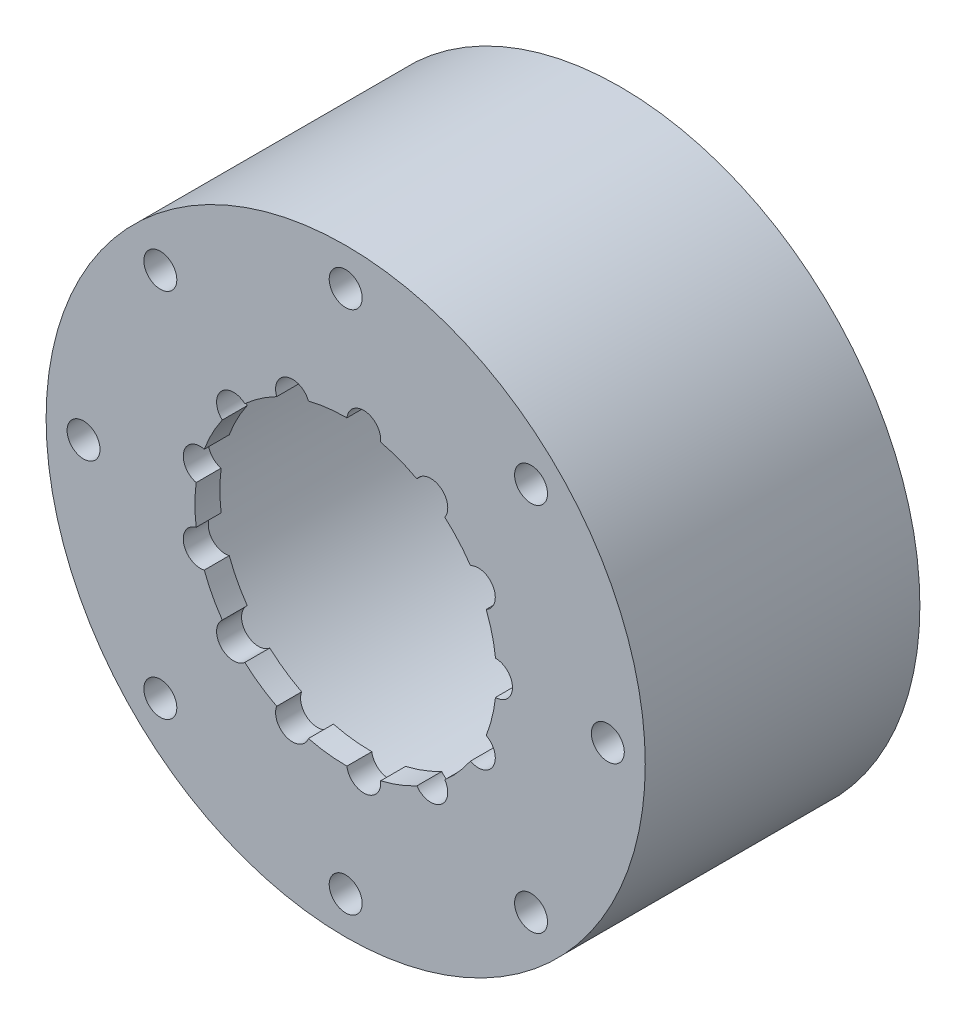
SolidWorks part; units mm, degrees
ref_plane "Front Plane" through (0, 0, 0) normal (0, 0, 1) x (1, 0, 0)
ref_plane "Top Plane" through (0, 0, 0) normal (0, 1, 0) x (1, 0, 0)
ref_plane "Right Plane" through (0, 0, 0) normal (1, 0, 0) x (0, 0, -1)
sketch "Sketch2" plane through (0, 0, 0) normal (0, 0, 1) x (1, 0, 0)
  circle A0 centre (0, 0) radius 60
  circle A1 centre (0, 0) radius 45
  dimension "D1" = 120
  dimension "D2" = 15
extrude "Boss-Extrude2" add sketch "Sketch2" along normal mid plane 50
sketch "Sketch3" plane through (0, 0, 25) normal (0, 0, 1) x (1, 0, 0)
  arc A0 (0.4234, 29.997) -> (-7.5898, 29.024) centre (0, 0) ccw construction
  circle A1 centre (0, 0) radius 60
  circle A2 centre (0, 0) radius 60
  arc A3 (29.8293, -3.1954) -> (29.8293, 3.1954) centre (30, 0) ccw construction
  arc A4 (24.9276, -16.6918) -> (27.8976, -11.033) centre (26.5637, -13.9417) ccw construction
  arc A5 (14.3152, -26.3643) -> (19.5748, -22.7338) centre (17.0419, -24.6895) ccw construction
  arc A6 (0.4234, -29.997) -> (6.7677, -29.2267) centre (3.6161, -29.7813) ccw construction
  arc A7 (-13.5654, -26.7578) -> (-7.5898, -29.024) centre (-10.6381, -28.0505) ccw construction
  arc A8 (-24.4465, -17.3887) -> (-20.2086, -22.1723) centre (-22.4553, -19.8937) ccw construction
  arc A9 (-29.7273, -4.036) -> (-28.1978, -10.2412) centre (-29.1283, -7.1795) ccw construction
  arc A10 (-28.1978, 10.2412) -> (-29.7273, 4.036) centre (-29.1283, 7.1795) ccw construction
  arc A11 (-20.2086, 22.1723) -> (-24.4465, 17.3887) centre (-22.4553, 19.8937) ccw construction
  arc A12 (-7.5898, 29.024) -> (-13.5654, 26.7578) centre (-10.6381, 28.0505) ccw construction
  arc A13 (6.7677, 29.2267) -> (0.4234, 29.997) centre (3.6161, 29.7813) ccw construction
  arc A14 (19.5748, 22.7338) -> (14.3152, 26.3643) centre (17.0419, 24.6895) ccw construction
  arc A15 (27.8976, 11.033) -> (24.9276, 16.6918) centre (26.5637, 13.9417) ccw construction
  arc A16 (14.3152, 26.3643) -> (6.7677, 29.2267) centre (0, 0) ccw construction
  arc A17 (24.9276, 16.6918) -> (19.5748, 22.7338) centre (0, 0) ccw construction
  arc A18 (29.8293, 3.1954) -> (27.8976, 11.033) centre (0, 0) ccw construction
  arc A19 (27.8976, -11.033) -> (29.8293, -3.1954) centre (0, 0) ccw construction
  arc A20 (19.5748, -22.7338) -> (24.9276, -16.6918) centre (0, 0) ccw construction
  arc A21 (6.7677, -29.2267) -> (14.3152, -26.3643) centre (0, 0) ccw construction
  arc A22 (-7.5898, -29.024) -> (0.4234, -29.997) centre (0, 0) ccw construction
  arc A23 (-20.2086, -22.1723) -> (-13.5654, -26.7578) centre (0, 0) ccw construction
  arc A24 (-28.1978, -10.2412) -> (-24.4465, -17.3887) centre (0, 0) ccw construction
  arc A25 (-29.7273, 4.036) -> (-29.7273, -4.036) centre (0, 0) ccw construction
  arc A26 (-24.4465, 17.3887) -> (-28.1978, 10.2412) centre (0, 0) ccw construction
  arc A27 (-13.5654, 26.7578) -> (-20.2086, 22.1723) centre (0, 0) ccw construction
  arc A28 (24.9907, 16.956) -> (19.8446, 22.7647) centre (0, 0) ccw
  arc A29 (19.8446, 22.7647) -> (14.2483, 26.6275) centre (17.0419, 24.6895) ccw
  arc A30 (14.2483, 26.6275) -> (6.9923, 29.3794) centre (0, 0) ccw
  arc A31 (6.9923, 29.3794) -> (0.2419, 30.199) centre (3.6161, 29.7813) ccw
  arc A32 (0.2419, 30.199) -> (-7.4619, 29.2636) centre (0, 0) ccw
  arc A33 (-7.4619, 29.2636) -> (-13.82, 26.8523) centre (-10.6381, 28.0505) ccw
  arc A34 (-13.82, 26.8523) -> (-20.2067, 22.4439) centre (0, 0) ccw
  arc A35 (-20.2067, 22.4439) -> (-24.7159, 17.3541) centre (-22.4553, 19.8937) ccw
  arc A36 (-24.7159, 17.3541) -> (-28.3224, 10.4826) centre (0, 0) ccw
  arc A37 (-28.3224, 10.4826) -> (-29.9497, 3.8802) centre (-29.1283, 7.1795) ccw
  arc A38 (-29.9497, 3.8802) -> (-29.9497, -3.8802) centre (0, 0) ccw
  arc A39 (-29.9497, -3.8802) -> (-28.3224, -10.4826) centre (-29.1283, -7.1795) ccw
  arc A40 (-28.3224, -10.4826) -> (-24.7159, -17.3541) centre (0, 0) ccw
  arc A41 (-24.7159, -17.3541) -> (-20.2067, -22.4439) centre (-22.4553, -19.8937) ccw
  arc A42 (-20.2067, -22.4439) -> (-13.82, -26.8523) centre (0, 0) ccw
  arc A43 (-13.82, -26.8523) -> (-7.4619, -29.2636) centre (-10.6381, -28.0505) ccw
  arc A44 (-7.4619, -29.2636) -> (0.2419, -30.199) centre (0, 0) ccw
  arc A45 (0.2419, -30.199) -> (6.9923, -29.3794) centre (3.6161, -29.7813) ccw
  arc A46 (6.9923, -29.3794) -> (14.2483, -26.6275) centre (0, 0) ccw
  arc A47 (14.2483, -26.6275) -> (19.8446, -22.7647) centre (17.0419, -24.6895) ccw
  arc A48 (19.8446, -22.7647) -> (24.9907, -16.956) centre (0, 0) ccw
  arc A49 (24.9907, -16.956) -> (28.1508, -10.9349) centre (26.5637, -13.9417) ccw
  arc A50 (28.1508, -10.9349) -> (30.008, -3.4) centre (0, 0) ccw
  arc A51 (30.008, -3.4) -> (30.008, 3.4) centre (30, 0) ccw
  arc A52 (30.008, 3.4) -> (28.1508, 10.9349) centre (0, 0) ccw
  arc A53 (28.1508, 10.9349) -> (24.9907, 16.956) centre (26.5637, 13.9417) ccw
  point P33 (0, 0)
  dimension "D2" = 60
  dimension "D3" = 6.4
  dimension "D1" = 0
  dimension "D5" = 0.2
  dimension "D4" = 13
extrude "Boss-Extrude3" add sketch "Sketch3" along normal blind 5
sketch "Sketch8" plane through (0, 0, 30) normal (0, 0, 1) x (1, 0, 0)
  circle A0 centre (0, 0) radius 52.5
  circle A1 centre (0, 0) radius 60 construction
  point P12 (0, 52.5)
  point P19 (37.1231, 37.1231)
  point P20 (52.5, 0)
  point P21 (37.1231, -37.1231)
  point P22 (0, -52.5)
  point P23 (-37.1231, -37.1231)
  point P24 (-52.5, 0)
  point P25 (-37.1231, 37.1231)
  dimension "D1" = 7.5
  dimension "D2" = 8
hole_wizard "M6 Clearance Hole1" positions "Sketch8" profile "Sketch7" hole size "M6" standard "ISO" end condition through all
sketch "Sketch7" plane through (-37.1231, 37.1231, 30) normal (1, 0, 0) x (0, -1, 0)
  line L0 (0, 0) -> (0, 55)
  line L1 (0, 55) -> (3.3, 55)
  line L2 (3.3, 55) -> (3.3, 0)
  line L5 (3.3, 0) -> (0, 0)
  line L11 (0, -6.35) -> (0, 107.95) construction
  dimension "Thru Hole Dia." = 6.6
  dimension "Thru Hole Depth" = 55
